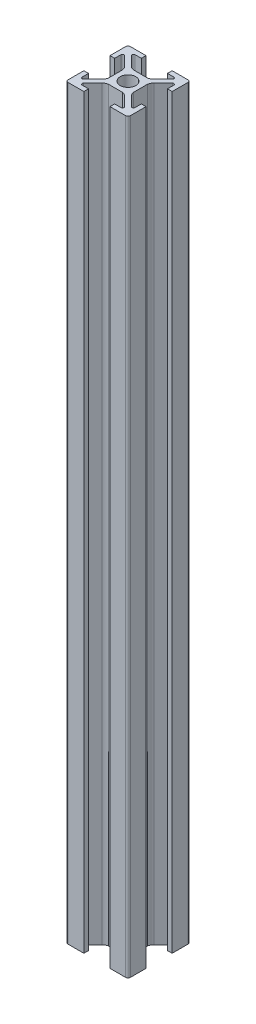
SolidWorks part; units mm, degrees
ref_plane "Front Plane" through (0, 0, 0) normal (0, 0, 1) x (1, 0, 0)
ref_plane "Top Plane" through (0, 0, 0) normal (0, 1, 0) x (1, 0, 0)
ref_plane "Right Plane" through (0, 0, 0) normal (1, 0, 0) x (0, 0, -1)
sketch "Sketch1" plane through (0, 0, 0) normal (0, 1, 0) x (1, 0, 0)
  line L0 (-3.611, 4.6716) -> (-6.5858, 7.6464)
  line L1 (9.25, -10) -> (4.2, -10)
  line L2 (10, -9.25) -> (10, -4.2)
  line L3 (9.25, 10) -> (4.2, 10)
  line L4 (-10, -9.25) -> (-10, -4.2)
  line L5 (10, -10) -> (-10, 10) construction
  line L6 (10, 10) -> (-10, -10) construction
  line L7 (2.2681, -4) -> (-2.2681, -4)
  line L8 (4, -2.2681) -> (4, 2.2681)
  line L9 (2.2681, 4) -> (-2.2681, 4)
  line L10 (-4, -2.2681) -> (-4, 2.2681)
  line L11 (4, -4) -> (-4, 4) construction
  line L12 (4, 4) -> (-4, -4) construction
  line L13 (-6.2322, 8.5) -> (-4.2, 8.5)
  line L14 (-4.2, 8.5) -> (-4.2, 10)
  line L15 (4.6716, 3.611) -> (7.6464, 6.5858)
  line L16 (8.5, 6.2322) -> (8.5, 4.2)
  line L17 (8.5, 4.2) -> (10, 4.2)
  line L18 (4.2, 8.5) -> (4.2, 10)
  line L19 (-8.5, 4.2) -> (-10, 4.2)
  line L20 (-8.5, 6.2322) -> (-8.5, 4.2)
  line L21 (-4.6716, 3.611) -> (-7.6464, 6.5858)
  line L22 (0, 10) -> (0, -10) construction
  line L23 (6.2322, 8.5) -> (4.2, 8.5)
  line L24 (3.611, 4.6716) -> (6.5858, 7.6464)
  line L25 (-55, 0) -> (55, 0) construction
  line L26 (3.611, -4.6716) -> (6.5858, -7.6464)
  line L27 (6.2322, -8.5) -> (4.2, -8.5)
  line L28 (-4.6716, -3.611) -> (-7.6464, -6.5858)
  line L29 (-8.5, -6.2322) -> (-8.5, -4.2)
  line L30 (-8.5, -4.2) -> (-10, -4.2)
  line L31 (4.2, -8.5) -> (4.2, -10)
  line L32 (8.5, -4.2) -> (10, -4.2)
  line L33 (8.5, -6.2322) -> (8.5, -4.2)
  line L34 (4.6716, -3.611) -> (7.6464, -6.5858)
  line L35 (-4.2, -8.5) -> (-4.2, -10)
  line L36 (-6.2322, -8.5) -> (-4.2, -8.5)
  line L37 (2.2681, -4) -> (-2.2681, -4)
  line L38 (10, -10) -> (4.2, -10)
  line L39 (-3.611, -4.6716) -> (-6.5858, -7.6464)
  line L40 (-4.2, 10) -> (-9.25, 10)
  line L41 (-10, 4.2) -> (-10, 9.25)
  line L42 (-4.2, -10) -> (-9.25, -10)
  line L43 (-4.2, -10) -> (-10, -10)
  line L44 (10, 4.2) -> (10, 9.25)
  circle A0 centre (0, 0) radius 2.5
  arc A1 (-8.5, 6.2322) -> (-7.6464, 6.5858) centre (-8, 6.2322) cw
  arc A2 (-6.5858, 7.6464) -> (-6.2322, 8.5) centre (-6.2322, 8) cw
  arc A3 (-3.611, 4.6716) -> (-2.2681, 4) centre (-1.7294, 6.7555) ccw
  arc A4 (-4.6716, 3.611) -> (-4, 2.2681) centre (-6.7555, 1.7294) cw
  arc A5 (4.6716, 3.611) -> (4, 2.2681) centre (6.7555, 1.7294) ccw
  arc A6 (3.611, 4.6716) -> (2.2681, 4) centre (1.7294, 6.7555) cw
  arc A7 (6.5858, 7.6464) -> (6.2322, 8.5) centre (6.2322, 8) ccw
  arc A8 (8.5, 6.2322) -> (7.6464, 6.5858) centre (8, 6.2322) ccw
  arc A9 (8.5, -6.2322) -> (7.6464, -6.5858) centre (8, -6.2322) cw
  arc A10 (6.5858, -7.6464) -> (6.2322, -8.5) centre (6.2322, -8) cw
  arc A11 (3.611, -4.6716) -> (2.2681, -4) centre (1.7294, -6.7555) ccw
  arc A12 (4.6716, -3.611) -> (4, -2.2681) centre (6.7555, -1.7294) cw
  arc A13 (-4.6716, -3.611) -> (-4, -2.2681) centre (-6.7555, -1.7294) ccw
  arc A14 (-3.611, -4.6716) -> (-2.2681, -4) centre (-1.7294, -6.7555) cw
  arc A15 (-6.5858, -7.6464) -> (-6.2322, -8.5) centre (-6.2322, -8) ccw
  arc A16 (-8.5, -6.2322) -> (-7.6464, -6.5858) centre (-8, -6.2322) ccw
  arc A17 (-9.25, -10) -> (-10, -9.25) centre (-9.25, -9.25) cw
  arc A18 (9.25, -10) -> (10, -9.25) centre (9.25, -9.25) ccw
  arc A19 (10, 9.25) -> (9.25, 10) centre (9.25, 9.25) ccw
  arc A20 (-9.25, 10) -> (-10, 9.25) centre (-9.25, 9.25) ccw
  point P0 (0, 0)
  point P18 (-8.5, 7.4393)
  point P24 (-7.4393, 8.5)
  point P50 (7.4393, 8.5)
  point P51 (8.5, 7.4393)
  point P86 (8.5, -7.4393)
  point P87 (7.4393, -8.5)
  point P88 (-7.4393, -8.5)
  point P89 (-8.5, -7.4393)
  dimension "D2" = 5
  dimension "D7" = 0.5
  dimension "D8" = 0.75
  dimension "D1" = 20
  dimension "D3" = 8
  dimension "D4" = 1.5
  dimension "D5" = 1.5
  dimension "D6" = 8.4
extrude "Boss-Extrude1" add sketch "Sketch1" along normal blind 240 contours L40 A20 L41 L19 L20 A1 L21 A4 L10 A13 L28 A16 L29 L30 L4 A17 L42 L35 L36 A15 L39 A14 L7 A11 L26 A10 L27 L31 L1 A18 L2 L32 L33 A9 L34 A12 L8 A5 L15 A8 L16 L17 L44 A19 L3 L18 L23 A7 L24 A6 L9
